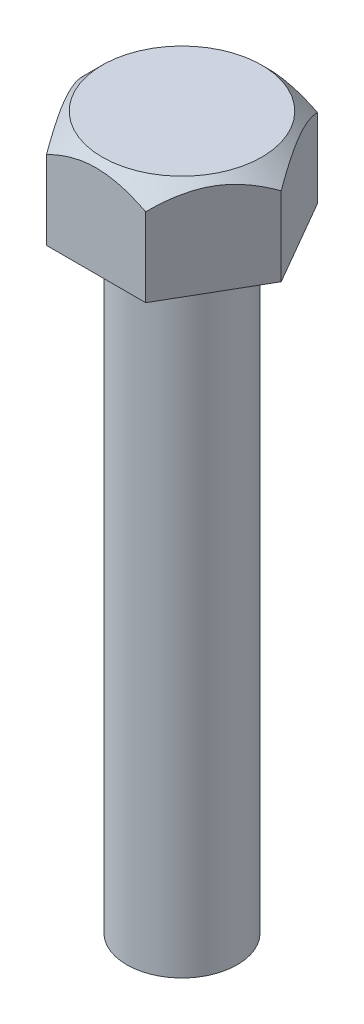
SolidWorks part; units mm, degrees
ref_plane "Front Plane" through (0, 0, 0) normal (0, 0, 1) x (1, 0, 0)
ref_plane "Top Plane" through (0, 0, 0) normal (0, 1, 0) x (1, 0, 0)
ref_plane "Right Plane" through (0, 0, 0) normal (1, 0, 0) x (0, 0, -1)
sketch "Sketch1" plane through (0, 0, 0) normal (0, 1, 0) x (1, 0, 0)
  circle A0 centre (0, 0) radius 2.25
  dimension "D1" = 4.5
extrude "Boss-Extrude1" add sketch "Sketch1" along normal blind 25
sketch "Sketch2" plane through (0, 25, 0) normal (0, 1, 0) x (1, 0, 0)
  line L1 (4.0415, 0) -> (2.0207, 3.5)
  line L2 (2.0207, 3.5) -> (-2.0207, 3.5)
  line L3 (-2.0207, 3.5) -> (-4.0415, 0)
  line L4 (-4.0415, 0) -> (-2.0207, -3.5)
  line L5 (-2.0207, -3.5) -> (2.0207, -3.5)
  line L6 (2.0207, -3.5) -> (4.0415, 0)
  point P0 (0, 0)
  dimension "D1" = 7
  dimension "D2" = 4.0415
extrude "Boss-Extrude2" add sketch "Sketch2" along normal blind 4
sketch "Sketch3" plane through (0, 29, 0) normal (0, 1, 0) x (1, 0, 0)
  circle A0 centre (0, 0) radius 3.25
  dimension "D1" = 6.5
extrude "Cut-Extrude1" cut sketch "Sketch3" against normal blind 4 draft 45 flip side to cut
